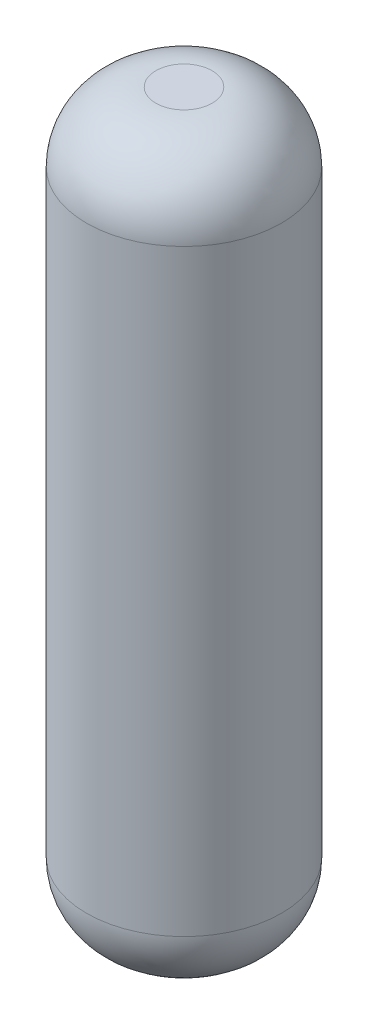
SolidWorks part; units mm, degrees
ref_plane "Front Plane" through (0, 0, 0) normal (0, 0, 1) x (1, 0, 0)
ref_plane "Top Plane" through (0, 0, 0) normal (0, 1, 0) x (1, 0, 0)
ref_plane "Right Plane" through (0, 0, 0) normal (1, 0, 0) x (0, 0, -1)
sketch "Sketch1" plane through (0, 0, 0) normal (0, 1, 0) x (1, 0, 0)
  circle A0 centre (0, 0) radius 57.15
  dimension "D1" = 114.3
extrude "Boss-Extrude1" add sketch "Sketch1" along normal blind 431.8
fillet "Fillet1" radius 40.64 2 edges at (0, 0, 57.15) (0, 431.8, 57.15)
